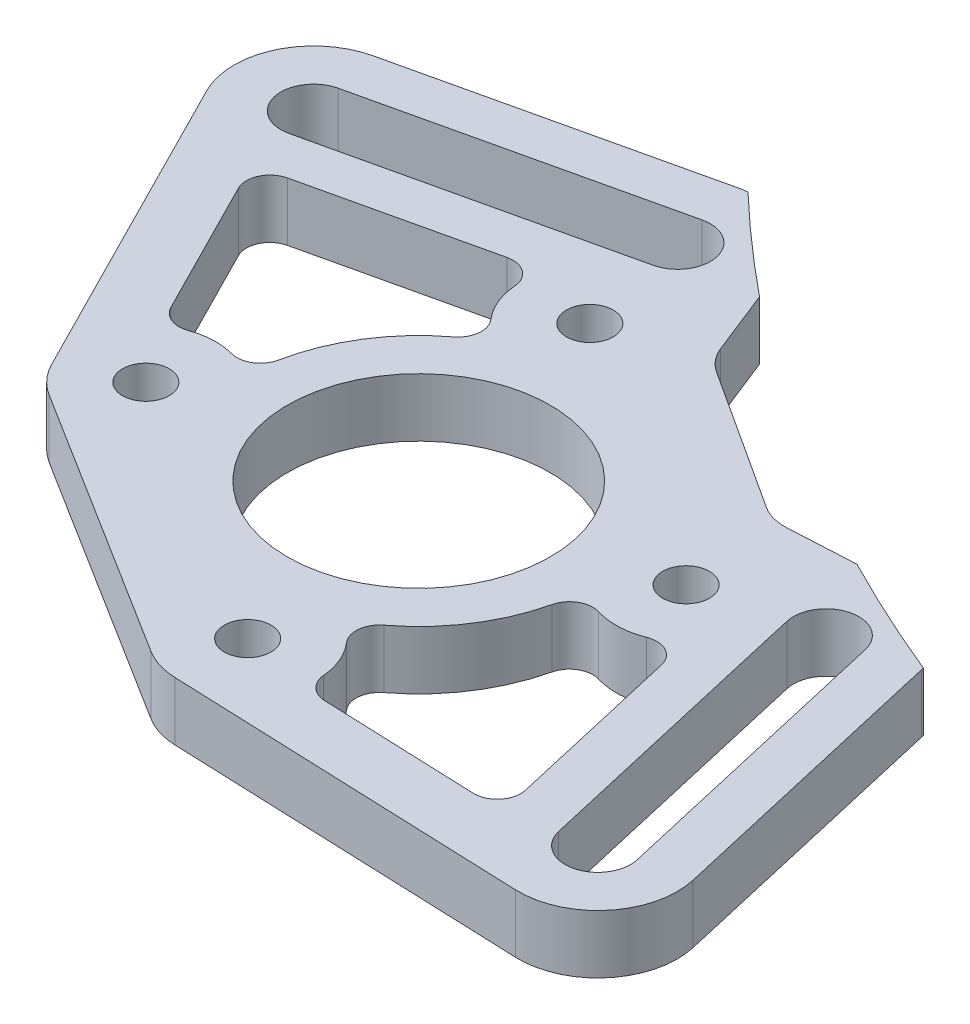
SolidWorks part; units mm, degrees
material "Polyester Resin"
ref_plane "Front Plane" through (0, 0, 0) normal (0, 0, 1) x (1, 0, 0)
ref_plane "Top Plane" through (0, 0, 0) normal (0, 1, 0) x (1, 0, 0)
ref_plane "Right Plane" through (0, 0, 0) normal (1, 0, 0) x (0, 0, -1)
sketch "Sketch1" plane through (0, 0, 0) normal (0, 1, 0) x (1, 0, 0)
  line L0 (9.2897, 14.4451) -> (11.6941, 18.1838) construction
  line L2 (-10.3015, 44.9223) -> (-42.4861, 37.5417)
  line L3 (45.0868, 9.5277) -> (52.4673, -22.6569)
  line L4 (-5.5326, 24.1261) -> (24.2906, 4.7587) construction
  line L5 (-5.5326, 24.1261) -> (5.5326, -24.1261) construction
  line L6 (36.6692, 7.5974) -> (44.0498, -24.5872) construction
  line L7 (40.1353, 8.3922) -> (47.5158, -23.7924)
  line L8 (33.2032, 6.8025) -> (40.5838, -25.382)
  line L9 (24.2906, 4.7587) -> (36.6692, 7.5974) construction
  line L10 (-6.9454, 30.2884) -> (30.3335, 6.0792) construction
  line L11 (30.3335, 6.0792) -> (6.1243, -31.1997) construction
  line L12 (6.1243, -31.1997) -> (-31.1546, -6.9905) construction
  line L13 (-31.1546, -6.9905) -> (-6.9454, 30.2884) construction
  line L14 (-5.5326, 24.1261) -> (-8.3712, 36.5048) construction
  line L15 (-8.3712, 36.5048) -> (-40.5558, 29.1242) construction
  line L16 (9.2897, 14.4451) -> (0, 0) construction
  line L17 (-7.5764, 33.0387) -> (-39.761, 25.6582)
  line L18 (-9.1661, 39.9708) -> (-41.3507, 32.5902)
  line L19 (-55, 0) -> (55, 0) construction
  line L21 (-48.2586, 25.2194) -> (-30.9226, -8.978)
  line L22 (-28.1736, -11.9887) -> (1.4851, -30.5822)
  line L23 (5.2404, -31.7405) -> (43.7187, -33.2169)
  line L24 (36.2135, 16.2213) -> (24.4027, 15.5971)
  line L25 (-0.3414, 39.6831) -> (3.9502, 28.8409)
  line L26 (21.3678, 16.4096) -> (5.9069, 26.4501)
  line L27 (-6.4409, 28.0872) -> (-38.6255, 20.7067) construction
  line L28 (28.2517, 5.6671) -> (35.6323, -26.5175) construction
  arc A6 (-7.5764, 33.0387) -> (-9.1661, 39.9708) centre (-8.3712, 36.5048) ccw
  arc A7 (-41.3507, 32.5902) -> (-39.761, 25.6582) centre (-40.5558, 29.1242) ccw
  circle A8 centre (-5.5326, 24.1261) radius 2.54
  circle A9 centre (24.2906, 4.7587) radius 2.54
  circle A10 centre (5.5326, -24.1261) radius 2.54
  circle A11 centre (-24.1261, -5.5326) radius 2.54
  circle A12 centre (0, 0) radius 14.2875
  circle A13 centre (0, 0) radius 21.0058 construction
  arc A14 (40.1353, 8.3922) -> (33.2032, 6.8025) centre (36.6692, 7.5974) ccw
  arc A15 (40.5838, -25.382) -> (47.5158, -23.7924) centre (44.0498, -24.5872) ccw
  circle A16 centre (44.0498, -24.5872) radius 11.1125 construction
  circle A17 centre (0, 0) radius 24.7523 construction
  arc A18 (-42.4861, 37.5417) -> (-48.2586, 25.2194) centre (-40.5558, 29.1242) ccw
  arc A19 (-0.3414, 39.6831) -> (-10.3015, 44.9223) centre (-8.3712, 36.5048) ccw
  arc A20 (43.7187, -33.2169) -> (52.4673, -22.6569) centre (44.0498, -24.5872) ccw
  arc A21 (45.0868, 9.5277) -> (36.2135, 16.2213) centre (36.6692, 7.5974) ccw
  arc A22 (1.4851, -30.5822) -> (5.2404, -31.7405) centre (5.5326, -24.1261) ccw
  arc A23 (-30.9226, -8.978) -> (-28.1736, -11.9887) centre (-24.1261, -5.5326) ccw
  arc A26 (-42.4861, 37.5417) -> (-38.6255, 20.7067) centre (-40.5558, 29.1242) ccw construction
  circle A27 centre (-24.1261, -5.5326) radius 7.62 construction
  circle A28 centre (5.5326, -24.1261) radius 7.62 construction
  arc A29 (35.6323, -26.5175) -> (52.4673, -22.6569) centre (44.0498, -24.5872) ccw construction
  arc A30 (-6.4409, 28.0872) -> (-10.3015, 44.9223) centre (-8.3712, 36.5048) ccw construction
  arc A31 (45.0868, 9.5277) -> (28.2517, 5.6671) centre (36.6692, 7.5974) ccw construction
  arc A32 (21.3678, 16.4096) -> (24.4027, 15.5971) centre (24.1346, 20.6701) ccw
  arc A33 (5.9069, 26.4501) -> (3.9502, 28.8409) centre (8.6736, 30.7105) cw
  point P20 (11.6941, 18.1838)
  point P39 (40.3595, -8.4949)
  point P49 (-24.4635, 32.8145)
  dimension "D4" = 5.08
  dimension "D5" = 28.575
  dimension "D6" = 42.0116
  dimension "D13" = 49.5046
  dimension "D26" = 5.08
  dimension "D3" = 35.56
  dimension "D7" = 7.112
  dimension "D8" = 33.02
  dimension "D9" = 12.7
  dimension "D10" = 7.112
  dimension "D11" = 33.02
  dimension "D12" = 12.7
  dimension "D14" = 44.45
  dimension "D15" = 44.45
  dimension "D16" = 4.3987
  dimension "D17" = 17.7037
  dimension "D18" = 5.08
  dimension "D19" = 17.1744
  dimension "D21" = 147
  dimension "D22" = 5.08
  dimension "D25" = 25.4
  dimension "D20" = 90
  dimension "D23" = 5.08
  dimension "D24" = 5.08
extrude "Boss-Extrude1" add sketch "Sketch1" along normal blind 6.35
sketch "Sketch3" plane through (0, 6.35, 0) normal (0, 1, 0) x (1, 0, 0)
  line L3 (28.2517, 5.6671) -> (35.6323, -26.5175)
  line L4 (29.6925, -0.6156) -> (35.6323, -26.5175)
  line L10 (111.5007, 171.696) -> (0, 0) construction
  line L11 (21.3678, 16.4096) -> (5.9069, 26.4501) construction
  line L13 (-38.6255, 20.7067) -> (-6.4409, 28.0872)
  line L14 (-38.6255, 20.7067) -> (-12.7237, 26.6465)
  line L16 (-42.5948, 28.0906) -> (-25.2588, -6.1068)
  line L17 (-24.8006, -6.6086) -> (4.858, -25.2021)
  line L18 (5.4839, -25.3951) -> (43.9621, -26.8715)
  line L19 (46.278, -24.0763) -> (38.8974, 8.1083)
  line L20 (36.5486, 9.8802) -> (24.7378, 9.256)
  line L21 (17.9094, 11.084) -> (2.4484, 21.1245)
  line L22 (-1.9541, 26.5038) -> (-6.2457, 37.3461)
  line L23 (-8.8822, 38.7329) -> (-41.0668, 31.3524)
  line L24 (-38.8293, 20.6626) -> (-28.6561, 0.5947)
  line L26 (12.9918, -25.6832) -> (35.6403, -26.5522)
  circle A2 centre (0, 0) radius 19.3675
  arc A3 (-8.8108, 17.2473) -> (-19.363, 0.4154) centre (0, 0) ccw
  arc A4 (8.8108, -17.2473) -> (19.3399, -1.034) centre (0, 0) ccw
  arc A5 (35.6323, -26.5175) -> (52.4673, -22.6569) centre (44.0498, -24.5872) ccw
  arc A6 (45.0868, 9.5277) -> (28.2517, 5.6671) centre (36.6692, 7.5974) ccw
  arc A7 (35.6323, -26.5175) -> (35.6403, -26.5522) centre (44.0498, -24.5872) ccw
  circle A14 centre (111.5007, 171.696) radius 175
  arc A15 (-6.4409, 28.0872) -> (-10.3015, 44.9223) centre (-8.3712, 36.5048) ccw
  arc A16 (-41.0668, 31.3524) -> (-42.5948, 28.0906) centre (-40.5558, 29.1242) ccw
  arc A17 (-25.2588, -6.1068) -> (-24.8006, -6.6086) centre (-24.1261, -5.5326) ccw
  arc A18 (4.858, -25.2021) -> (5.4839, -25.3951) centre (5.5326, -24.1261) ccw
  arc A19 (43.9621, -26.8715) -> (46.278, -24.0763) centre (44.0498, -24.5872) ccw
  arc A20 (38.8974, 8.1083) -> (36.5486, 9.8802) centre (36.6692, 7.5974) ccw
  arc A21 (17.9094, 11.084) -> (24.7378, 9.256) centre (24.1346, 20.6701) ccw
  arc A22 (-1.9541, 26.5038) -> (2.4484, 21.1245) centre (8.6736, 30.7105) ccw
  arc A23 (-6.2457, 37.3461) -> (-8.8822, 38.7329) centre (-8.3712, 36.5048) ccw
  arc A32 (-42.4861, 37.5417) -> (-38.6255, 20.7067) centre (-40.5558, 29.1242) ccw
  arc A34 (-38.8293, 20.6626) -> (-38.6255, 20.7067) centre (-40.5558, 29.1242) ccw
  circle A38 centre (-5.5326, 24.1261) radius 7.62
  arc A39 (-12.7237, 26.6465) -> (-8.8108, 17.2473) centre (-5.5326, 24.1261) ccw
  circle A41 centre (-24.1261, -5.5326) radius 7.62
  arc A42 (-19.363, 0.4154) -> (-28.6561, 0.5947) centre (-24.1261, -5.5326) ccw
  circle A44 centre (24.2906, 4.7587) radius 7.62
  arc A45 (19.3399, -1.034) -> (29.6925, -0.6156) centre (24.2906, 4.7587) ccw
  circle A47 centre (5.5326, -24.1261) radius 7.62
  arc A48 (12.9918, -25.6832) -> (8.8108, -17.2473) centre (5.5326, -24.1261) ccw
  dimension "D9" = 350
  dimension "D10" = 204.724
  dimension "D1" = 6.35
  dimension "D2" = 5.08
  dimension "D3" = 5.08
  dimension "D4" = 5.08
  dimension "D5" = 5.08
  dimension "D6" = 5.08
  dimension "D7" = 5.08
  dimension "D8" = 5.08
extrude "Cut-Extrude1" cut sketch "Sketch3" against normal through all
fillet "Fillet1" radius 2.54 10 edges at (35.6403, 3.175, 26.5522) (8.8108, 3.175, 17.2473) (12.9918, 3.175, 25.6832) (29.6925, 3.175, 0.6156) (19.3399, 3.175, 1.034) (-38.8293, 3.175, -20.6626) (-28.6561, 3.175, -0.5947) (-19.363, 3.175, -0.4154) (-8.8108, 3.175, -17.2473) (-12.7237, 3.175, -26.6465)
